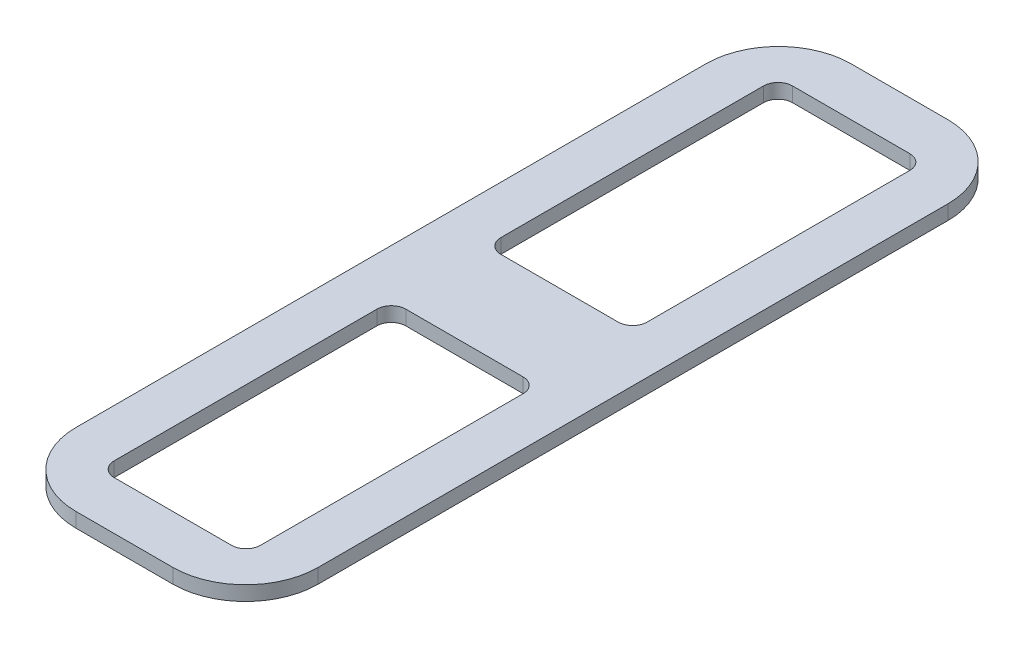
SolidWorks part; units mm, degrees
ref_plane "Front Plane" through (0, 0, 0) normal (0, 0, 1) x (1, 0, 0)
ref_plane "Top Plane" through (0, 0, 0) normal (0, 1, 0) x (1, 0, 0)
ref_plane "Right Plane" through (0, 0, 0) normal (1, 0, 0) x (0, 0, -1)
sketch "Sketch1" plane through (0, 0, 0) normal (0, 1, 0) x (1, 0, 0)
  line L1 (-25, 80) -> (25, 80)
  line L2 (-25, 80) -> (-25, -80)
  line L3 (-25, -80) -> (25, -80)
  line L4 (25, 80) -> (25, -80)
  line L5 (-25, 80) -> (25, -80) construction
  line L6 (-25, -80) -> (25, 80) construction
  point P0 (0, 0)
extrude "Boss-Extrude1" add sketch "Sketch1" along normal blind 3
fillet "Fillet2" radius 15 4 edges at (25, 1.5, -80) (-25, 1.5, -80) (25, 1.5, 80) (-25, 1.5, 80)
sketch "Sketch3" plane through (0, 3, 0) normal (0, 1, 0) x (1, 0, 0)
  line L1 (-12.1, 70) -> (12.1, 70)
  line L2 (-15.1, 67) -> (-15.1, 12.8)
  line L3 (-12.1, 9.8) -> (12.1, 9.8)
  line L4 (15.1, 67) -> (15.1, 12.8)
  line L5 (-15.1, 70) -> (15.1, 9.8) construction
  line L6 (-15.1, 9.8) -> (15.1, 70) construction
  line L7 (10, 80) -> (-10, 80) construction
  line L8 (25, -65) -> (25, 65) construction
  line L9 (-25, 65) -> (-25, -65) construction
  arc A0 (12.1, 9.8) -> (15.1, 12.8) centre (12.1, 12.8) ccw
  arc A1 (-15.1, 12.8) -> (-12.1, 9.8) centre (-12.1, 12.8) ccw
  arc A2 (12.1, 70) -> (15.1, 67) centre (12.1, 67) cw
  arc A3 (-12.1, 70) -> (-15.1, 67) centre (-12.1, 67) ccw
  point P0 (0, 20.2528)
  point P18 (0, 20.2528)
  point P20 (0, 0)
  dimension "D1" = 3
  dimension "D2" = 30.2
  dimension "D3" = 60.2
  dimension "D4" = 10
  dimension "D5" = 9.9
  dimension "D6" = 9.9
extrude "Cut-Extrude1" cut sketch "Sketch3" against normal through all contours L2 A1 L3 A0 L4 A2 L1 A3
mirror "Mirror1" about plane through (0, 0, 0) normal (0, 0, 1) of "Cut-Extrude1"
